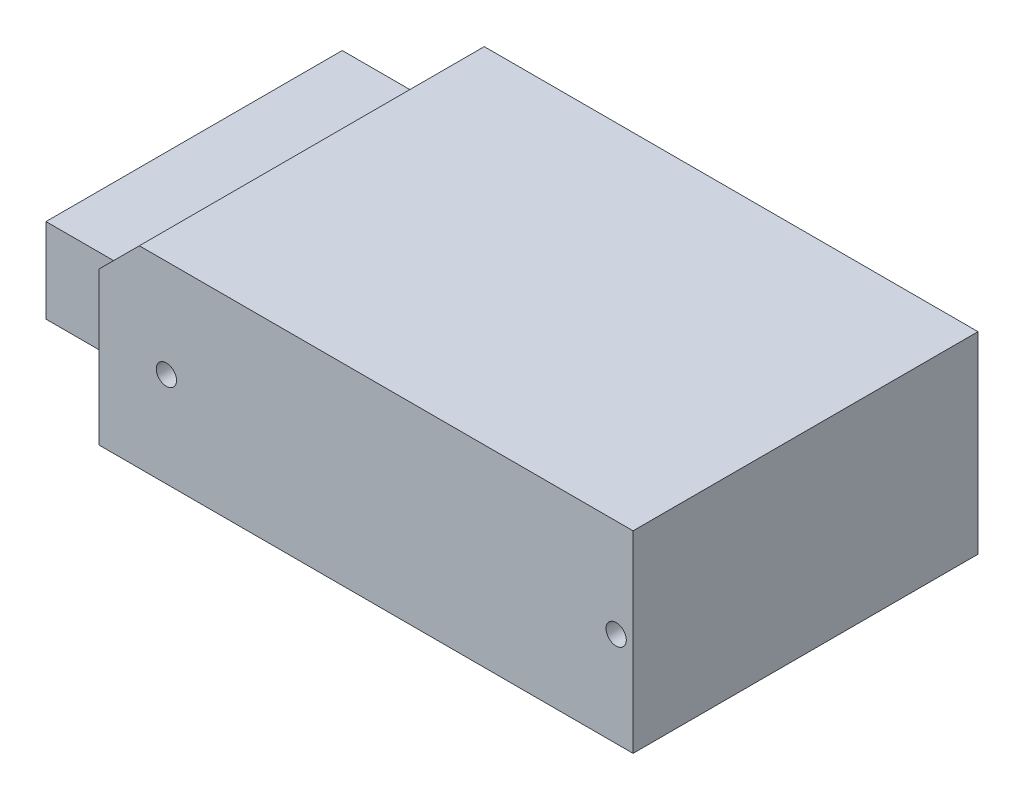
SolidWorks part; units mm, degrees
ref_plane "Front" through (0, 0, 0) normal (0, 0, 1) x (1, 0, 0)
ref_plane "Top" through (0, 0, 0) normal (0, 1, 0) x (1, 0, 0)
ref_plane "Right" through (0, 0, 0) normal (1, 0, 0) x (0, 0, -1)
sketch "Sketch1" plane through (0, 0, 0) normal (0, 1, 0) x (1, 0, 0)
  line L1 (-39.5, -25.5) -> (39.5, -25.5)
  line L2 (-39.5, -25.5) -> (-39.5, 25.5)
  line L3 (-39.5, 25.5) -> (39.5, 25.5)
  line L4 (39.5, -25.5) -> (39.5, 25.5)
  line L5 (-39.5, -25.5) -> (39.5, 25.5) construction
  line L6 (-39.5, 25.5) -> (39.5, -25.5) construction
  point P0 (0, 0)
  dimension "D1" = 51
  dimension "D2" = 79
extrude "Boss-Extrude1" add sketch "Sketch1" along normal blind 28.5
sketch "Sketch2" plane through (-39.5, 0, 0) normal (-1, 0, 0) x (0, 0, 1)
  line L0 (-25.5, 28.5) -> (-25.5, 0) construction
  line L1 (-25.5, 17.5) -> (18.3, 17.5)
  line L2 (-25.5, 17.5) -> (-25.5, 5)
  line L3 (-25.5, 5) -> (18.3, 5)
  line L4 (18.3, 17.5) -> (18.3, 5)
  line L5 (-25.5, 0) -> (25.5, 0) construction
  dimension "D1" = 5
  dimension "D2" = 43.8
  dimension "D3" = 12.5
extrude "Boss-Extrude2" add sketch "Sketch2" along normal blind 15
sketch "Sketch3" plane through (0, 0, 25.5) normal (0, 0, 1) x (1, 0, 0)
  line L0 (-39.5, 28.5) -> (-39.5, 22.5)
  line L1 (-39.5, 28.5) -> (-39.5, 0) construction
  line L2 (-39.5, 22.5) -> (-33.5, 28.5)
  line L3 (-39.5, 28.5) -> (39.5, 28.5) construction
  line L4 (-33.5, 28.5) -> (-39.5, 28.5)
  dimension "D1" = 6
  dimension "D2" = 6
extrude "Cut-Extrude1" cut sketch "Sketch3" against normal through all
sketch "Sketch4" plane through (0, 0, 25.5) normal (0, 0, 1) x (1, 0, 0)
  line L0 (-39.5, 22.5) -> (-39.5, 0) construction
  line L1 (-39.5, 0) -> (39.5, 0) construction
  circle A0 centre (-29.5, 14) radius 1.5
  circle A1 centre (37, 14) radius 1.5
  dimension "D1" = 3
  dimension "D2" = 3
  dimension "D3" = 10
  dimension "D4" = 14
  dimension "D5" = 66.5
  dimension "D6" = 14
extrude "Cut-Extrude2" cut sketch "Sketch4" against normal blind 15
sketch "Sketch5" plane through (0, 0, 0) normal (0, -1, 0) x (1, 0, 0)
  line L0 (-39.5, -25.5) -> (-39.5, 25.5) construction
  line L1 (39.5, -25.5) -> (-39.5, -25.5) construction
  circle A0 centre (-26, 0) radius 1.5
  circle A1 centre (29, 0) radius 1.5
  dimension "D5" = 3
  dimension "D6" = 3
  dimension "D1" = 13.5
  dimension "D2" = 55
  dimension "D3" = 25.5
  dimension "D4" = 25.5
extrude "Cut-Extrude3" cut sketch "Sketch5" against normal blind 15
